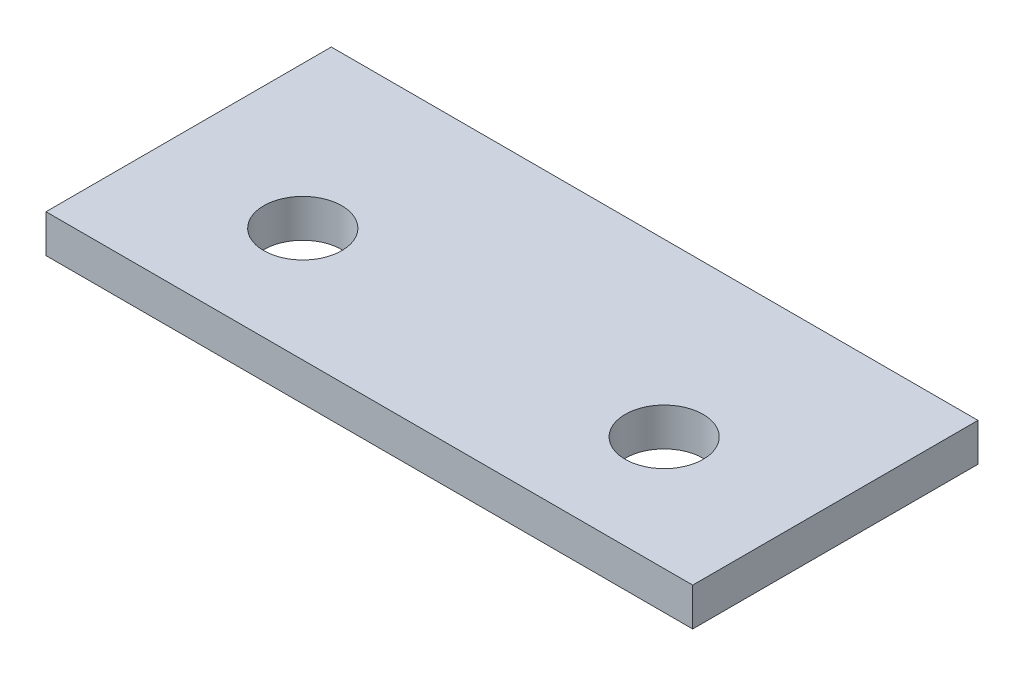
SolidWorks part; units mm, degrees
ref_plane "Спереди" through (0, 0, 0) normal (0, 0, 1) x (1, 0, 0)
ref_plane "Сверху" through (0, 0, 0) normal (0, 1, 0) x (1, 0, 0)
ref_plane "Справа" through (0, 0, 0) normal (1, 0, 0) x (0, 0, -1)
sketch "Эскиз1" plane through (0, 0, 0) normal (0, 1, 0) x (1, 0, 0)
  line L0 (34, 33.1062) -> (34, -33.1062) construction
  line L1 (0, 0) -> (68, 0)
  line L2 (0, 0) -> (0, 30)
  line L3 (0, 30) -> (68, 30)
  line L4 (68, 0) -> (68, 30)
  circle A0 centre (15, 12) radius 4.1
  circle A1 centre (53, 12) radius 4.1
  point P11 (34, 0)
  point P12 (32.4557, 33.1062)
extrude "Бобышка-Вытянуть1" add sketch "Эскиз1" along normal blind 4
